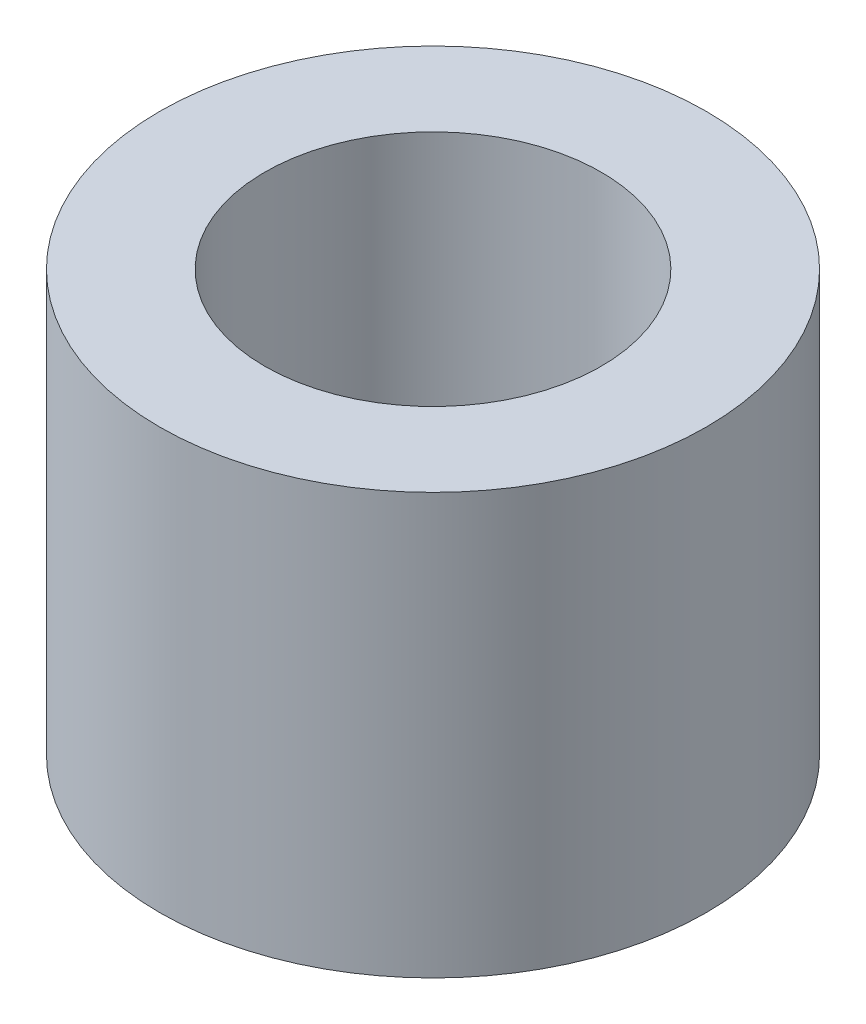
SolidWorks part; units mm, degrees
ref_plane "Front Plane" through (0, 0, 0) normal (0, 0, 1) x (1, 0, 0)
ref_plane "Top Plane" through (0, 0, 0) normal (0, 1, 0) x (1, 0, 0)
ref_plane "Right Plane" through (0, 0, 0) normal (1, 0, 0) x (0, 0, -1)
sketch "Sketch1" plane through (0, 0, 0) normal (0, 1, 0) x (1, 0, 0)
  circle A0 centre (0, 0) radius 1.6
  circle A1 centre (0, 0) radius 2.6
  dimension "D1" = 3.2
  dimension "D2" = 5.2
extrude "Boss-Extrude1" add sketch "Sketch1" along normal blind 4
